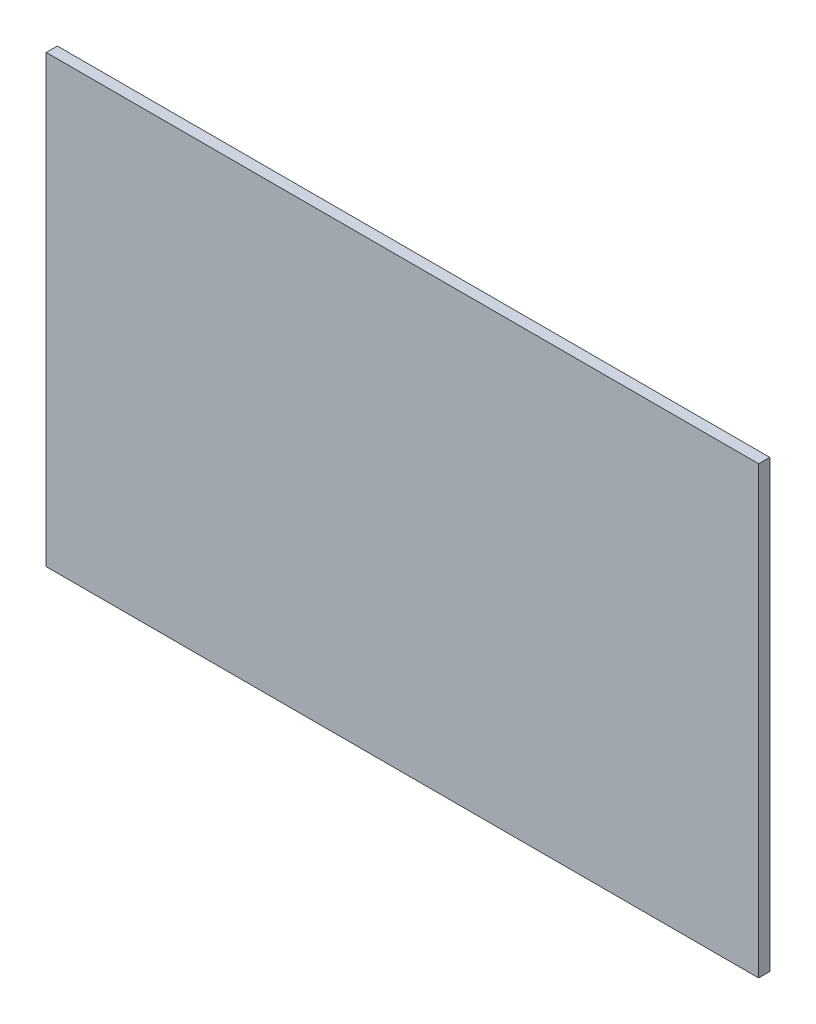
SolidWorks part; units mm, degrees
material "Oak"
ref_plane "Front" through (0, 0, 0) normal (0, 0, 1) x (1, 0, 0)
ref_plane "Top" through (0, 0, 0) normal (0, 1, 0) x (1, 0, 0)
ref_plane "Right" through (0, 0, 0) normal (1, 0, 0) x (0, 0, -1)
sketch "Sketch1" plane through (0, 0, 0) normal (0, 0, 1) x (1, 0, 0)
  line L1 (-203.2, 254) -> (203.2, 254)
  line L2 (-203.2, 254) -> (-203.2, 0)
  line L3 (-203.2, 0) -> (203.2, 0)
  line L4 (203.2, 254) -> (203.2, 0)
  point P4 (0, 0)
  dimension "D1" = 406.4
  dimension "D2" = 254
extrude "Boss-Extrude1" add sketch "Sketch1" along normal blind 6.35
